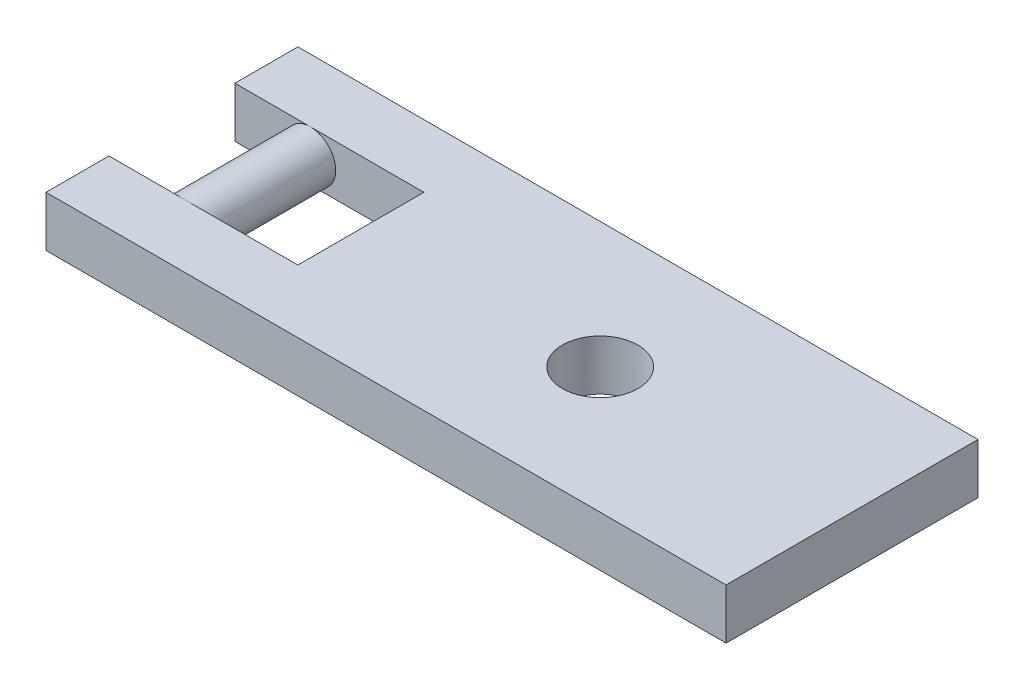
SolidWorks part; units mm, degrees
ref_plane "Ön Düzlem" through (0, 0, 0) normal (0, 0, 1) x (1, 0, 0)
ref_plane "Üst Düzlem" through (0, 0, 0) normal (0, 1, 0) x (1, 0, 0)
ref_plane "Sağ Düzlem" through (0, 0, 0) normal (1, 0, 0) x (0, 0, -1)
sketch "Çizim1" plane through (0, 0, 0) normal (0, 0, 1) x (1, 0, 0)
  line L0 (0, 38.4038) -> (0, -31.5962) construction
  line L1 (-4.7988, 38.4038) -> (-29.7988, 38.4038)
  line L3 (-4.7988, 40.4038) -> (-31.7988, 40.4038)
  line L4 (-31.7988, 40.4038) -> (-31.7988, 38.4038)
  line L6 (-4.7988, 40.4038) -> (-4.7988, 38.4038)
  line L7 (-29.7988, 38.4038) -> (-31.7988, 38.4038)
  line L9 (-29.7988, 38.4038) -> (-29.7988, -31.5962) construction
  line L11 (-31.7988, 40.4038) -> (-31.7988, -31.5962) construction
  dimension "D1" = 70
  dimension "D2" = 25
  dimension "D3" = 2
extrude "Yükseklik-Ekstrüzyon1" add sketch "Çizim1" along normal mid plane 10
sketch "Çizim2" plane through (0, 40.4038, 0) normal (0, 1, 0) x (1, 0, 0)
  line L5 (-31.7988, -5) -> (-31.7988, 5) construction
  line L6 (-24.2988, 2.5) -> (-39.2988, 2.5)
  line L8 (-24.2988, 2.5) -> (-24.2988, -2.5)
  line L9 (-24.2988, -2.5) -> (-39.2988, -2.5)
  line L10 (-39.2988, 2.5) -> (-39.2988, -2.5)
  line L11 (-24.2988, 2.5) -> (-39.2988, -2.5) construction
  line L12 (-24.2988, -2.5) -> (-39.2988, 2.5) construction
  point P0 (-31.7988, 0)
  dimension "D1" = 15
  dimension "D2" = 5
extrude "Kes-Ekstrüzyon1" cut sketch "Çizim2" against normal blind 10
sketch "Çizim4" plane through (0, 0, 0) normal (0, 0, 1) x (1, 0, 0)
  line L0 (-31.7988, 40.4038) -> (-31.7988, 38.4038) construction
  circle A0 centre (-28.7988, 39.4038) radius 1
  dimension "D2" = 2
  dimension "D1" = 3
extrude "Yükseklik-Ekstrüzyon2" add sketch "Çizim4" along normal mid plane 5
sketch "Çizim5" plane through (0, 40.4038, 0) normal (0, 1, 0) x (1, 0, 0)
  line L0 (-4.7988, -5) -> (-4.7988, 5) construction
  circle A0 centre (-14.7988, 0) radius 1.5
  dimension "D1" = 3
  dimension "D2" = 10
extrude "Kes-Ekstrüzyon2" cut sketch "Çizim5" against normal blind 5
